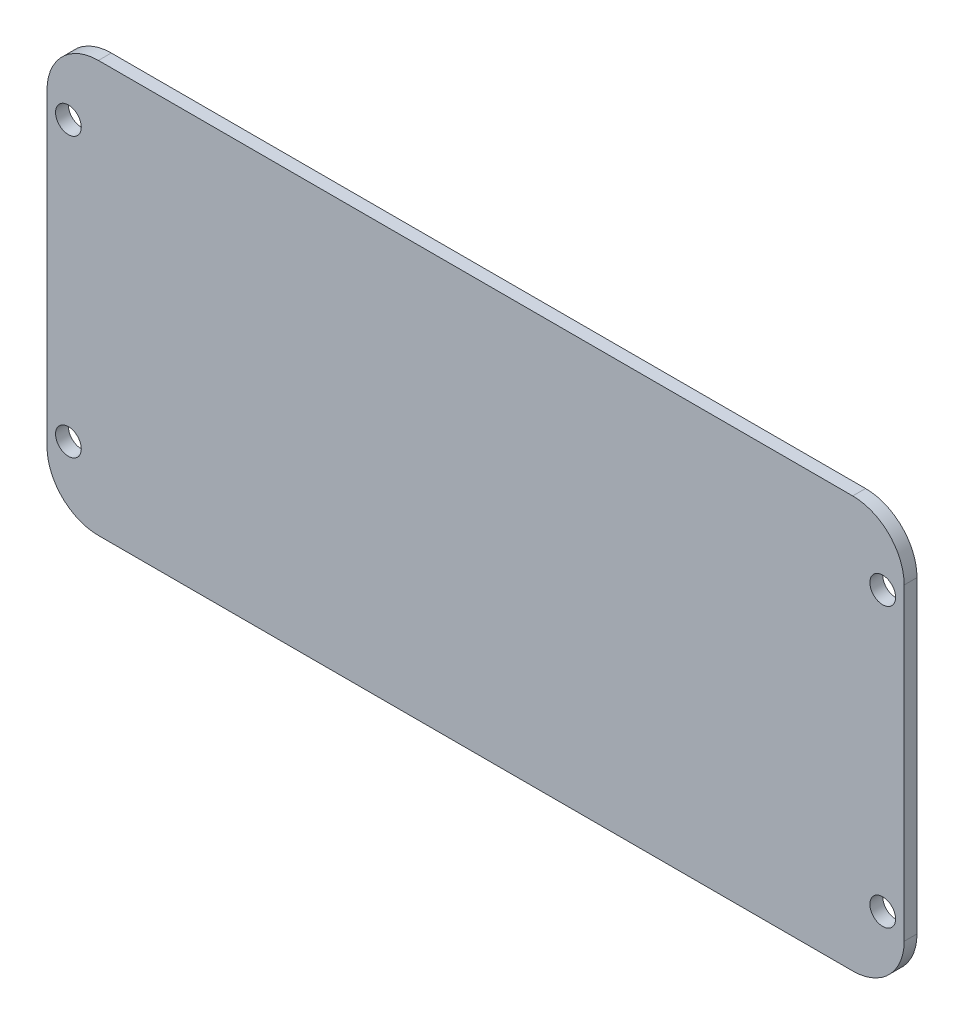
SolidWorks part; units mm, degrees
ref_plane "Alzado" through (0, 0, 0) normal (0, 0, 1) x (1, 0, 0)
ref_plane "Planta" through (0, 0, 0) normal (0, 1, 0) x (1, 0, 0)
ref_plane "Vista lateral" through (0, 0, 0) normal (1, 0, 0) x (0, 0, -1)
sketch "Croquis1" plane through (0, 0, 0) normal (0, 0, 1) x (1, 0, 0)
  line L0 (-38.5893, 20.8) -> (49.4107, 20.8)
  line L1 (55.4107, 14.8) -> (55.4107, -21.2)
  line L2 (49.4107, -27.2) -> (-38.5893, -27.2)
  line L3 (-44.5893, -21.2) -> (-44.5893, 14.8)
  line L4 (-42.0893, 13.05) -> (52.9107, 13.05) construction
  line L5 (52.9107, 13.05) -> (52.9107, -19.45) construction
  line L6 (52.9107, -19.45) -> (-42.0893, -19.45) construction
  line L7 (-42.0893, -19.45) -> (-42.0893, 13.05) construction
  line L8 (-44.5893, -3.2) -> (55.4107, -3.2) construction
  line L9 (-42.0893, -3.2) -> (52.9107, -3.2) construction
  circle A0 centre (-42.0893, 13.05) radius 1.5
  circle A1 centre (-42.0893, -19.45) radius 1.5
  circle A2 centre (52.9107, -19.45) radius 1.5
  circle A3 centre (52.9107, 13.05) radius 1.5
  arc A4 (55.4107, 14.8) -> (49.4107, 20.8) centre (49.4107, 14.8) ccw
  arc A5 (55.4107, -21.2) -> (49.4107, -27.2) centre (49.4107, -21.2) cw
  arc A6 (-38.5893, -27.2) -> (-44.5893, -21.2) centre (-38.5893, -21.2) cw
  arc A7 (-44.5893, 14.8) -> (-38.5893, 20.8) centre (-38.5893, 14.8) cw
  point P18 (55.4107, 20.8)
  point P23 (-44.5893, -27.2)
  point P26 (-44.5893, 20.8)
  dimension "D3" = 32.5
  dimension "D4" = 95
  dimension "D5" = 2.5
  dimension "D6" = 6
  dimension "D1" = 48
  dimension "D2" = 100
extrude "Saliente-Extruir1" add sketch "Croquis1" along normal blind 1.5
